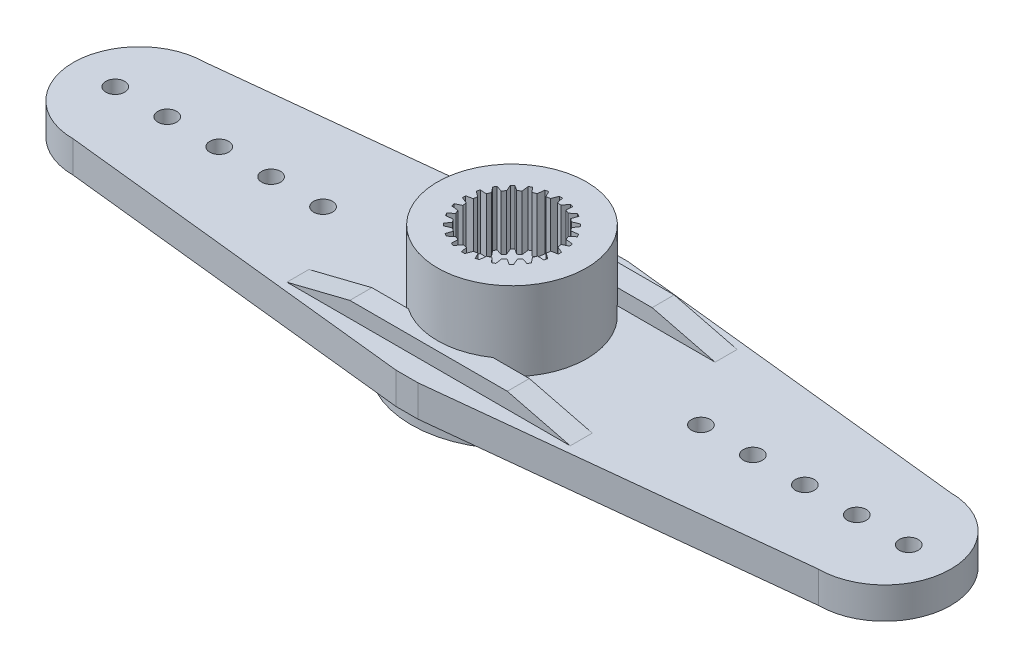
SolidWorks part; units mm, degrees
ref_plane "Ön Düzlem" through (0, 0, 0) normal (0, 0, 1) x (1, 0, 0)
ref_plane "Üst Düzlem" through (0, 0, 0) normal (0, 1, 0) x (1, 0, 0)
ref_plane "Sağ Düzlem" through (0, 0, 0) normal (1, 0, 0) x (0, 0, -1)
sketch "Çizim1" plane through (0, 0, 0) normal (0, 1, 0) x (1, 0, 0)
  circle A0 centre (0, 0) radius 6.4
  circle A1 centre (0, 0) radius 4.735
  dimension "D1" = 9.47
extrude "Yükseklik-Ekstrüzyon1" add sketch "Çizim1" along normal blind 2.8
sketch "Çizim3" plane through (0, 0, 0) normal (0, -1, 0) x (1, 0, 0)
  circle A0 centre (0, 0) radius 4.735
extrude "Yükseklik-Ekstrüzyon3" add sketch "Çizim3" against normal blind 7.8
ref_plane "Düzlem1" through (0, 0.8, 0) normal (0, -1, 0) x (-1, 0, 0)
sketch "Çizim6" plane through (0, 0.8, 0) normal (0, -1, 0) x (-1, 0, 0)
  line L0 (-0.7, 6.67) -> (0.7, 6.67)
  line L1 (0, 0) -> (23.67, 0) construction
  line L2 (0.7, 6.67) -> (23.67, 4.2)
  line L3 (-0.7, -6.67) -> (0.7, -6.67)
  line L4 (0.7, -6.67) -> (23.67, -4.2)
  line L5 (0, 0) -> (0, 6.4) construction
  line L6 (-0.7, -6.67) -> (-23.67, -4.2)
  line L7 (-0.7, 6.67) -> (-23.67, 4.2)
  arc A2 (23.67, -4.2) -> (23.67, 4.2) centre (23.67, 0) ccw
  circle A3 centre (12, 0) radius 0.6
  circle A5 centre (18.6, 0) radius 0.6
  circle A6 centre (21.9, 0) radius 0.6
  circle A7 centre (25.2, 0) radius 0.6
  circle A8 centre (15.3, 0) radius 0.6
  circle A9 centre (0, 0) radius 6.4 construction
  circle A10 centre (-12, 0) radius 0.6
  circle A11 centre (-15.3, 0) radius 0.6
  circle A12 centre (-18.6, 0) radius 0.6
  circle A13 centre (-21.9, 0) radius 0.6
  circle A14 centre (-25.2, 0) radius 0.6
  arc A15 (-23.67, -4.2) -> (-23.67, 4.2) centre (-23.67, 0) cw
  point P26 (0, -6.67)
  point P27 (0, 6.67)
  dimension "D1" = 12
  dimension "D2" = 3.3
  dimension "D3" = 3.3
  dimension "D4" = 3.3
  dimension "D5" = 3.3
extrude "Yükseklik-Ekstrüzyon5" add sketch "Çizim6" against normal up to surface (2 mm away) up to face at (0, 2.8, 6.4)
sketch "Çizim7" plane through (0, 0.8, 0) normal (0, -1, 0) x (-1, 0, 0)
  line L1 (-9, 5.3) -> (-3.5875, 5.3)
  line L2 (-9, 5.3) -> (-9, 3.9)
  line L3 (-9, 3.9) -> (-5.0744, 3.9)
  line L4 (9, 5.3) -> (9, 3.9)
  line L5 (-9, 0.6995) -> (-6.3617, 0.6995)
  line L6 (-9, 0.6995) -> (-9, -0.7005)
  line L7 (-9, -0.7005) -> (-6.3616, -0.7005)
  line L8 (9, 0.6995) -> (9, -0.7005)
  line L13 (9, -5.3) -> (9, -3.9)
  line L14 (-9, -3.9) -> (-5.0744, -3.9)
  line L15 (-9, -5.3) -> (-9, -3.9)
  line L16 (-9, -5.3) -> (-3.5875, -5.3)
  line L17 (5.0744, 3.9) -> (9, 3.9)
  line L18 (3.5875, 5.3) -> (9, 5.3)
  line L19 (6.3617, 0.6995) -> (9, 0.6995)
  line L20 (6.3616, -0.7005) -> (9, -0.7005)
  line L21 (5.0744, -3.9) -> (9, -3.9)
  line L22 (3.5875, -5.3) -> (9, -5.3)
  circle A0 centre (0, 0) radius 6.4
  point P28 (0, 0)
  point P29 (0, 0)
  dimension "D1" = 1.4
  dimension "D2" = 18
  dimension "D3" = 9
  dimension "D4" = 5.3
  dimension "D5" = 9
  dimension "D6" = 0.6995
extrude "Yükseklik-Ekstrüzyon6" add sketch "Çizim7" along normal blind 0.8 contours A0 L1 L2 L3 | A0 L5 L6 L7 | A0 L14 L15 L16 | A0 L22 L13 L21 | A0 L20 L8 L19 | A0 L17 L4 L18
sketch "Çizim8" plane through (0, 0, -3.9) normal (0, 0, 1) x (1, 0, 0)
  line L0 (-9, 0.8) -> (-9, 0)
  line L1 (-9, 0) -> (-5.0744, 0)
  line L2 (-5.0744, 0) -> (-9, 0.8)
extrude "Kes-Ekstrüzyon1" cut sketch "Çizim8" against normal blind 2
sketch "Çizim10" plane through (0, 0, 0.7005) normal (0, 0, 1) x (1, 0, 0)
  line L0 (-6.3616, 0) -> (-9, 0.8)
  line L1 (-9, 0.8) -> (-9, 0)
  line L2 (-9, 0) -> (-6.3616, 0)
extrude "Kes-Ekstrüzyon2" cut sketch "Çizim10" against normal blind 2
sketch "Çizim11" plane through (0, 0, 3.9) normal (0, 0, -1) x (-1, 0, 0)
  line L0 (9, 0.8) -> (9, 0)
  line L1 (9, 0) -> (5.0744, 0)
  line L2 (5.0744, 0) -> (9, 0.8)
extrude "Kes-Ekstrüzyon3" cut sketch "Çizim11" against normal blind 2
sketch "Çizim12" plane through (0, 0, 3.9) normal (0, 0, -1) x (-1, 0, 0)
  line L0 (-5.0744, 0) -> (-9, 0.8)
  line L1 (-9, 0.8) -> (-9, 0)
  line L2 (-9, 0) -> (-5.0744, 0)
extrude "Kes-Ekstrüzyon4" cut sketch "Çizim12" against normal blind 2
sketch "Çizim13" plane through (0, 0, 0.7005) normal (0, 0, 1) x (1, 0, 0)
  line L0 (9, 0.8) -> (6.3616, 0)
  line L1 (6.3616, 0) -> (9, 0)
  line L2 (9, 0) -> (9, 0.8)
extrude "Kes-Ekstrüzyon5" cut sketch "Çizim13" against normal blind 2
sketch "Çizim14" plane through (0, 0, -3.9) normal (0, 0, 1) x (1, 0, 0)
  line L0 (9, 0) -> (9, 0.8)
  line L1 (9, 0.8) -> (5.0744, 0)
  line L2 (5.0744, 0) -> (9, 0)
extrude "Kes-Ekstrüzyon6" cut sketch "Çizim14" against normal blind 2
sketch "Çizim16" plane through (0, 0, 0) normal (0, -1, 0) x (-1, 0, 0)
  circle A0 centre (0, 0) radius 3.1
extrude "Kes-Ekstrüzyon8" cut sketch "Çizim16" against normal blind 3
ref_plane "Düzlem2" through (0, 0, 0) normal (0, 0, -1) x (-1, 0, 0)
sketch "Çizim17" plane through (0, 0, 0) normal (0, 0, -1) x (-1, 0, 0)
  line L0 (0, 0) -> (0, 1.8)
  line L1 (0, 1.8) -> (-3.1, 1.8)
  line L2 (0, 0) -> (-3.9, 0)
  line L3 (-5.0744, 0) -> (-3.5875, 0) construction
  line L4 (-3.9, 0) -> (-3.9, 1)
  line L5 (-3.9, 1) -> (-3.1, 1.8)
revolve "Kes-Döndür1" cut sketch "Çizim17" angle 360 about L0
sketch "Çizim18" plane through (0, 2.8, 0) normal (0, 1, 0) x (1, 0, 0)
  line L0 (0, 4.735) -> (0, 0) construction
  line L1 (-9, 5.3) -> (9, 5.3)
  line L2 (-9, 5.3) -> (-9, 3.9)
  line L3 (-9, 3.9) -> (9, 3.9)
  line L4 (9, 5.3) -> (9, 3.9)
  line L5 (0, 0) -> (4.735, 0) construction
  line L6 (3.1255, 0) -> (-3.1255, 0) construction
  line L7 (-9, -5.3) -> (-9, -3.9)
  line L8 (9, -5.3) -> (9, -3.9)
  line L9 (-9, -5.3) -> (9, -5.3)
  line L10 (-9, -3.9) -> (9, -3.9)
  circle A0 centre (0, 0) radius 4.735 construction
  circle A1 centre (0, 0) radius 4.735 construction
  dimension "D1" = 9
  dimension "D2" = 3.9
extrude "Yükseklik-Ekstrüzyon7" add sketch "Çizim18" along normal blind 1
sketch "Çizim19" plane through (0, 0, 5.3) normal (0, 0, 1) x (1, 0, 0)
  line L9 (-9, 3.8) -> (9, 3.8) construction
  line L10 (-5, 3.8) -> (-9, 3.8)
  line L12 (5, 3.8) -> (9, 3.8)
  line L13 (-5, 3.8) -> (-9, 2.8)
  line L14 (-9, 2.8) -> (-9, 3.8)
  line L15 (5, 3.8) -> (9, 2.8)
  line L16 (9, 2.8) -> (9, 3.8)
extrude "Kes-Ekstrüzyon11" cut sketch "Çizim19" against normal blind 12
sketch "Çizim20" plane through (0, 7.8, 0) normal (0, 1, 0) x (1, 0, 0)
  circle A0 centre (0, 0) radius 2.68
extrude "Kes-Ekstrüzyon13" cut sketch "Çizim20" against normal blind 3.5
sketch "Çizim21" plane through (0, 3, 0) normal (0, -1, 0) x (1, 0, 0)
  circle A0 centre (0, 0) radius 1.65
  dimension "D1" = 3.3
extrude "Kes-Ekstrüzyon14" cut sketch "Çizim21" against normal blind 3.5
sketch "Çizim22" plane through (0, 4.3, 0) normal (0, 1, 0) x (1, 0, 0)
  line L0 (-2.9346, 0.9236) -> (-2.5254, 0.8969)
  line L1 (-2.9899, 0.7247) -> (-2.6402, 0.4603)
  arc A0 (-2.9346, 0.9236) -> (-2.9899, 0.7247) centre (0, 0) ccw
  circle A2 centre (0, 0) radius 2.68 construction
  arc A3 (-2.6402, 0.4603) -> (-2.5254, 0.8969) centre (0, 0) cw
extrude "Kes-Ekstrüzyon16" cut sketch "Çizim22" along normal blind 12.5
pattern_circular "Dairesel Kaplama1" count 25 every 15 about axis through (0, 0, 0) along (0, 1, 0) of "Kes-Ekstrüzyon16"
